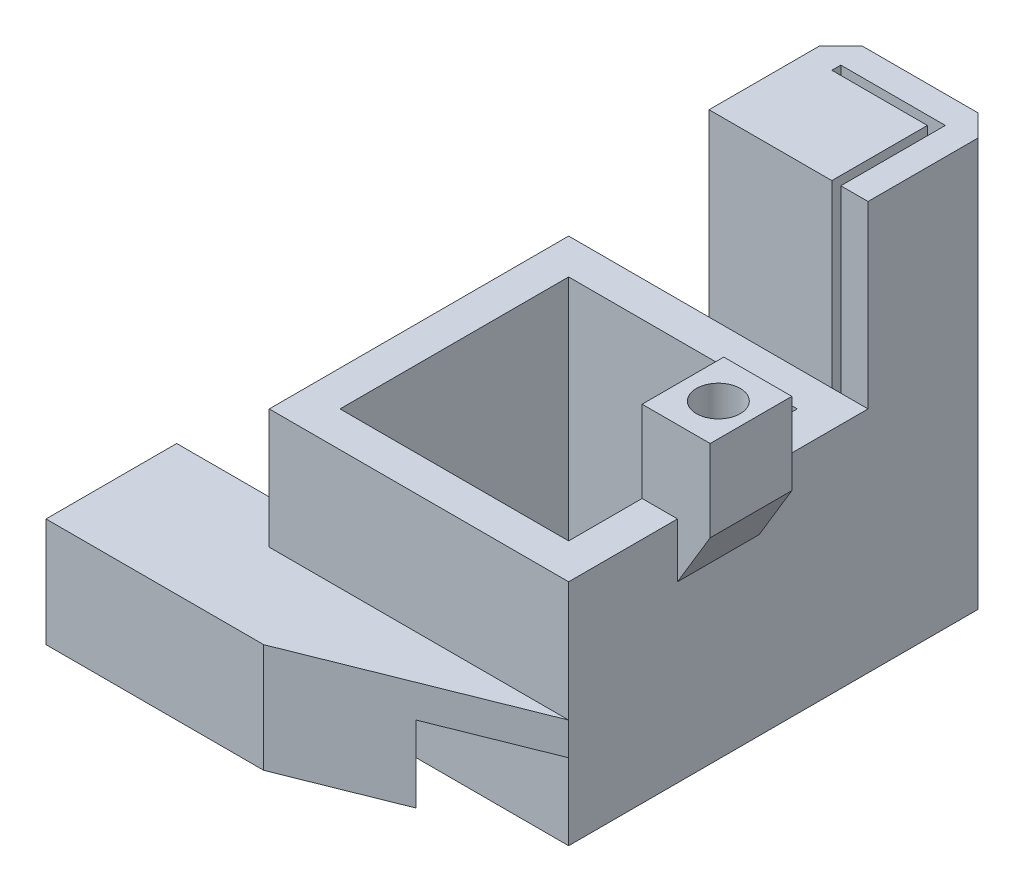
SolidWorks part; units mm, degrees
ref_plane "Front Plane" through (0, 0, 0) normal (0, 0, 1) x (1, 0, 0)
ref_plane "Top Plane" through (0, 0, 0) normal (0, 1, 0) x (1, 0, 0)
ref_plane "Right Plane" through (0, 0, 0) normal (1, 0, 0) x (0, 0, -1)
sketch "Sketch1" plane through (0, 0, 0) normal (0, 1, 0) x (1, 0, 0)
  line L1 (0, 0) -> (42, 0)
  line L2 (0, 0) -> (0, 42)
  line L3 (0, 42) -> (42, 42)
  line L4 (42, 0) -> (42, 42)
  line L5 (-6.5, -6.5) -> (48.5, -6.5)
  line L6 (-6.5, -6.5) -> (-6.5, 48.5)
  line L7 (-6.5, 48.5) -> (48.5, 48.5)
  line L8 (48.5, -6.5) -> (48.5, 48.5)
  dimension "D1" = 55
  dimension "D2" = 55
  dimension "D3" = 42
  dimension "D4" = 42
  dimension "D5" = 6.5
  dimension "D6" = 6.5
extrude "Boss-Extrude1" add sketch "Sketch1" along normal blind 42
sketch "Sketch2" plane through (0, 0, 0) normal (0, -1, 0) x (1, 0, 0)
  line L0 (5.96, 6.5) -> (5.96, 14.51)
  line L1 (-6.5, 6.5) -> (48.5, 6.5) construction
  line L2 (5.96, 14.51) -> (-31.5, 14.51)
  line L3 (-31.5, 14.51) -> (-31.5, 22.51)
  line L6 (-6.5, -21) -> (48.5, -21) construction
  line L7 (8.5, 22.51) -> (48.5, 6.5)
  line L8 (-31.5, 22.51) -> (8.5, 22.51)
  line L9 (-6.5, -48.5) -> (-6.5, 6.5) construction
  line L16 (48.5, 6.5) -> (5.96, 6.5)
  line L24 (-6.5, 6.5) -> (-31.5, 6.5)
  line L25 (-6.5, 6.5) -> (-6.5, -1.5)
  line L26 (-6.5, -1.5) -> (-31.5, -1.5)
  line L27 (-31.5, 6.5) -> (-31.5, -1.5)
  point P12 (-6.5, -21)
  dimension "D1" = 8.01
  dimension "D2" = 8
  dimension "D3" = 40
  dimension "D4" = 40
  dimension "D5" = 42.54
extrude "Boss-Extrude2" add sketch "Sketch2" against normal blind 20
sketch "Sketch3" plane through (0, 0, 0) normal (0, -1, 0) x (1, 0, 0)
  line L0 (48.5, -48.5) -> (48.5, -72.7)
  line L1 (48.5, -72.7) -> (19.3, -72.7)
  line L5 (48.5, -48.5) -> (-6.5, -48.5) construction
  line L6 (19.3, -48.5) -> (48.5, -48.5)
  line L7 (24.3, -66.05) -> (41.85, -66.05)
  line L8 (41.85, -66.05) -> (41.85, -48.5)
  line L9 (43.5, -48.5) -> (43.5, -67.7)
  line L10 (43.5, -67.7) -> (24.3, -67.7)
  line L11 (24.3, -66.05) -> (24.3, -67.7)
  line L16 (48.5, -68.7) -> (44.5, -72.7)
  line L17 (19.3, -72.7) -> (19.3, -48.5)
  line L18 (23.3, -72.7) -> (19.3, -68.7)
  line M16 (-6.5, -48.5) -> (48.5, -48.5)
  dimension "D1" = 1.65
  dimension "D2" = 1.65
  dimension "D3" = 19.2
  dimension "D4" = 5
  dimension "D5" = 4
  dimension "D6" = 5
  dimension "D7" = 5
  dimension "D8" = 4
  dimension "D9" = 4
  dimension "D10" = 4
extrude "Boss-Extrude3" add sketch "Sketch3" against normal blind 75 contours L18 L1 L16 L0 L9 L10 L11 L7 L8 L17 M16
sketch "Sketch5" plane through (0, 42, 0) normal (0, 1, 0) x (1, 0, 0)
  line L1 (48.5, -6.5) -> (48.5, 48.5) construction
  line L3 (42, 0) -> (42, 42) construction
  line L4 (42, 13.5) -> (54.5, 13.5)
  line L5 (42, 13.5) -> (42, 28.5)
  line L6 (42, 28.5) -> (54.5, 28.5)
  line L7 (54.5, 13.5) -> (54.5, 28.5)
  circle A0 centre (48.5, 21) radius 4.025
  point P10 (42, 21)
  dimension "D1" = 8.05
  dimension "D2" = 15
  dimension "D3" = 12.5
extrude "Boss-Extrude4" add sketch "Sketch5" along normal blind 15
sketch "Sketch6" plane through (0, 0, -13.5) normal (0, 0, 1) x (1, 0, 0)
  line L0 (54.5, 42) -> (48.5, 42)
  line L1 (48.5, 42) -> (48.5, 32)
  line L2 (48.5, 32) -> (54.5, 42)
  dimension "D1" = 10
extrude "Boss-Extrude5" add sketch "Sketch6" against normal up to surface (15 mm away) up to face at (48.3, 48, -28.5)
ref_plane "Plane1" through (0, 0, -21) normal (0, 0, -1) x (-1, 0, 0)
sketch "Sketch7" plane through (5.96, 0, 0) normal (-1, 0, 0) x (0, 0, 1)
  line L0 (14.51, 20) -> (14.51, 0) construction
  line L1 (6.5, 20) -> (14.51, 20)
  line L2 (6.5, 20) -> (6.5, 14)
  line L3 (6.5, 14) -> (14.51, 14)
  line L4 (14.51, 20) -> (14.51, 14)
  dimension "D1" = 6
extrude "Boss-Extrude6" add sketch "Sketch7" along normal up to surface (37.46 mm away) up to face at (-31.5, 10, 2.5)
sketch "Sketch8" plane through (5.96, 0, 0) normal (-1, 0, 0) x (0, 0, 1)
  line L1 (6.5, 14) -> (14.51, 14)
  line L2 (6.5, 14) -> (6.5, 0)
  line L3 (6.5, 0) -> (14.51, 0)
  line L4 (14.51, 14) -> (14.51, 0)
extrude "Cut-Extrude1" cut sketch "Sketch8" against normal through all
sketch "Sketch9" plane through (-6.5, 0, 0) normal (-1, 0, 0) x (0, 0, 1)
  line L0 (-1.5, 20) -> (-1.5, 0) construction
  line L1 (-48.5, 0) -> (-1.5, 0)
  line L2 (-48.5, 0) -> (-48.5, 4)
  line L3 (-48.5, 4) -> (-1.5, 4)
  line L4 (-1.5, 0) -> (-1.5, 4)
  dimension "D1" = 4
extrude "Boss-Extrude7" add sketch "Sketch9" along normal blind 10
